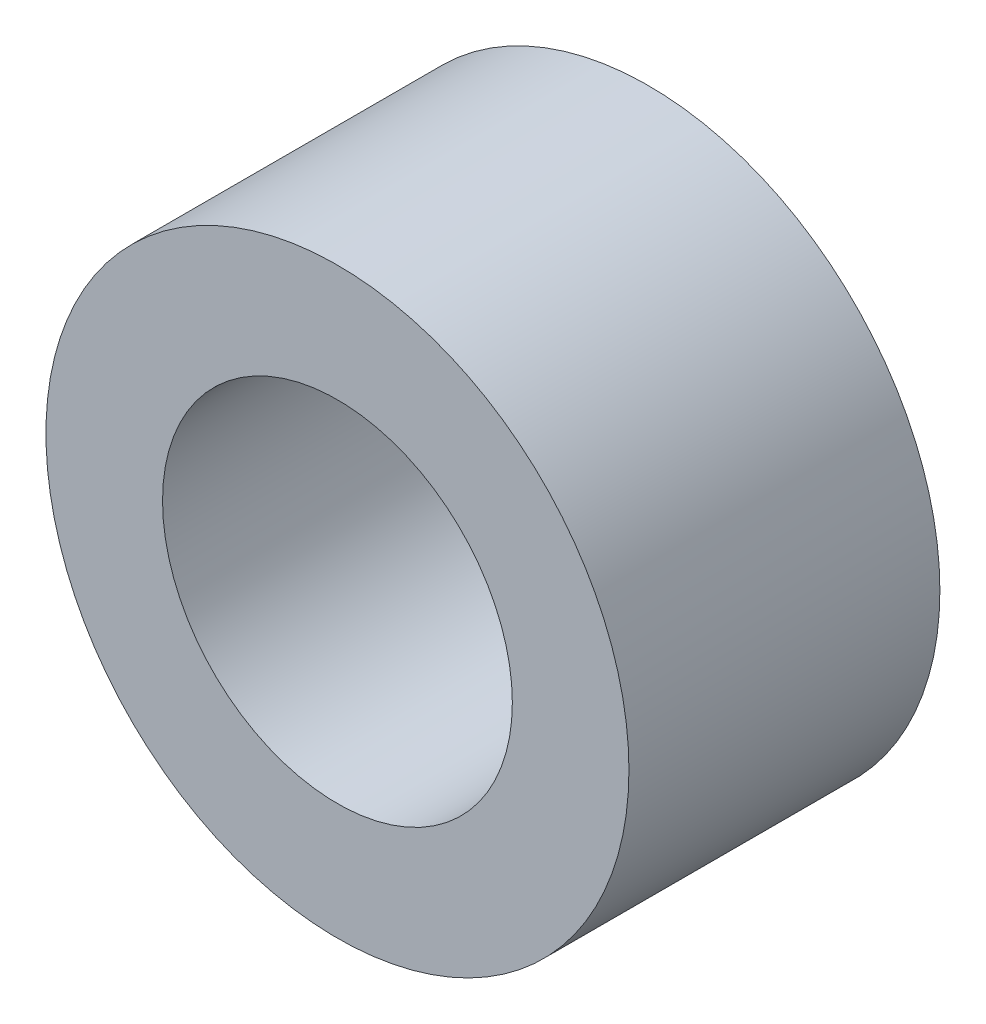
SolidWorks part; units mm, degrees
ref_plane "Front Plane" through (0, 0, 0) normal (0, 0, 1) x (1, 0, 0)
ref_plane "Top Plane" through (0, 0, 0) normal (0, 1, 0) x (1, 0, 0)
ref_plane "Right Plane" through (0, 0, 0) normal (1, 0, 0) x (0, 0, -1)
sketch "Sketch1" plane through (0, 0, 0) normal (0, 0, 1) x (1, 0, 0)
  circle A0 centre (0, 0) radius 2.25
  circle A1 centre (0, 0) radius 3.75
  dimension "D1" = 4.5
  dimension "D2" = 1.5
extrude "Boss-Extrude1" add sketch "Sketch1" along normal blind 4
